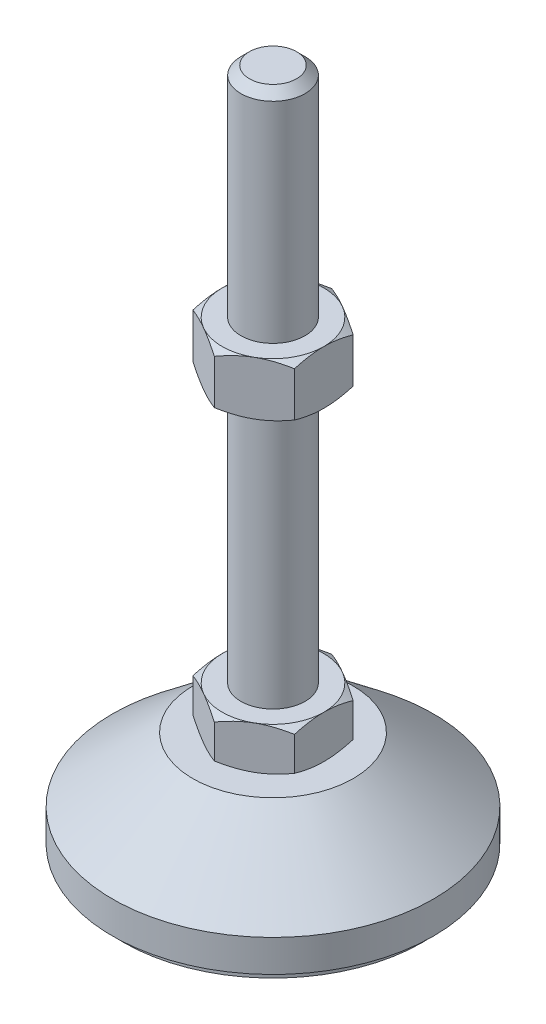
SolidWorks part; units mm, degrees
ref_plane "Спереди" through (0, 0, 0) normal (0, 0, 1) x (1, 0, 0)
ref_plane "Сверху" through (0, 0, 0) normal (0, 1, 0) x (1, 0, 0)
ref_plane "Справа" through (0, 0, 0) normal (1, 0, 0) x (0, 0, -1)
sketch "Эскиз1" plane through (0, 0, 0) normal (0, 0, 1) x (1, 0, 0)
  line L0 (0, 0) -> (-28, 0)
  line L1 (-28, 0) -> (-28, 2)
  line L2 (-28, 2) -> (-30, 2)
  line L3 (-30, 2) -> (-30, 8)
  line L4 (-30, 8) -> (-15, 20)
  line L5 (-15, 20) -> (-6, 20)
  line L12 (-6, 28) -> (-6, 126.4)
  line L13 (-6, 126.4) -> (-4.4, 128)
  line L14 (-4.4, 128) -> (0, 128)
  line L15 (0, 128) -> (0, 0) construction
  line L16 (-6, 20) -> (0, 20) construction
  line L17 (0, 0) -> (0, 128)
  line L18 (0, 0) -> (0, -7.9595) construction
  line L19 (-6, 28) -> (-6, 20)
  point P8 (-6, 77.2)
  point P23 (-10.5, 20)
  dimension "D1" = 12
  dimension "D2" = 20
  dimension "D3" = 8
  dimension "D4" = 60
  dimension "D5" = 6
  dimension "D6" = 1.6
  dimension "D7" = 45
  dimension "D8" = 30
  dimension "D9" = 2
  dimension "D10" = 100
  dimension "D11" = 6
revolve "Повернуть1" add sketch "Эскиз1" angle 360 about L17
sketch "Эскиз2" plane through (0, 20, 0) normal (0, 1, 0) x (1, 0, 0)
  line L1 (0, 10.9697) -> (-9.5, 5.4848)
  line L2 (-9.5, 5.4848) -> (-9.5, -5.4848)
  line L3 (-9.5, -5.4848) -> (0, -10.9697)
  line L4 (0, -10.9697) -> (9.5, -5.4848)
  line L5 (9.5, -5.4848) -> (9.5, 5.4848)
  line L6 (9.5, 5.4848) -> (0, 10.9697)
  circle A0 centre (0, 0) radius 9.5 construction
  dimension "D1" = 19
extrude "Бобышка-Вытянуть1" add sketch "Эскиз2" along normal up to vertex (8 mm away) up to point (-6, 28, 0)
ref_plane "Плоскость1" through (0, 77.2, 0) normal (0, 1, 0) x (1, 0, 0)
sketch "Эскиз3" plane through (0, 77.2, 0) normal (0, 1, 0) x (1, 0, 0)
  line L6 (9.5, 5.4848) -> (0, 10.9697)
  line L7 (0, 10.9697) -> (-9.5, 5.4848)
  line L8 (-9.5, 5.4848) -> (-9.5, -5.4848)
  line L9 (-9.5, -5.4848) -> (0, -10.9697)
  line L10 (0, -10.9697) -> (9.5, -5.4848)
  line L11 (9.5, -5.4848) -> (9.5, 5.4848)
  line L12 (9.5, 5.4848) -> (0, 10.9697)
  line L13 (0, 10.9697) -> (-9.5, 5.4848)
  line L14 (-9.5, 5.4848) -> (-9.5, -5.4848)
  line L15 (-9.5, -5.4848) -> (0, -10.9697)
  line L16 (0, -10.9697) -> (9.5, -5.4848)
  line L17 (9.5, -5.4848) -> (9.5, 5.4848)
  dimension "D1" = 0
extrude "Бобышка-Вытянуть2" add sketch "Эскиз3" along normal blind 10
sketch "Эскиз4" plane through (0, 0, 0) normal (0, 0, 1) x (1, 0, 0)
  line L0 (-9.5, 87.2) -> (-18.1603, 82.2)
  line L1 (-18.1603, 82.2) -> (-18.1603, 87.2)
  line L2 (-18.1603, 87.2) -> (-9.5, 87.2)
  line L3 (-18.1603, 82.2) -> (-9.5, 77.2)
  line L4 (50, 77.2) -> (-50, 77.2) construction
  line L5 (-9.5, 77.2) -> (-18.1603, 77.2)
  line L6 (-18.1603, 77.2) -> (-18.1603, 82.2)
  line L7 (-9.5, 87.2) -> (-9.5, 77.2) construction
  line L8 (-9.5, 28) -> (-16.4282, 28)
  line L9 (-16.4282, 28) -> (-16.4282, 24)
  line L10 (-16.4282, 24) -> (-9.5, 28)
  line L11 (-9.5, 20) -> (-16.4282, 24)
  line L12 (-16.4282, 24) -> (-16.4282, 20)
  line L13 (-16.4282, 20) -> (-9.5, 20)
  line L14 (0, 128) -> (0, 96.3793) construction
  dimension "D1" = 30
  dimension "D2" = 30
revolve "Вырез-Повернуть2" cut sketch "Эскиз4" angle 360 about L14
